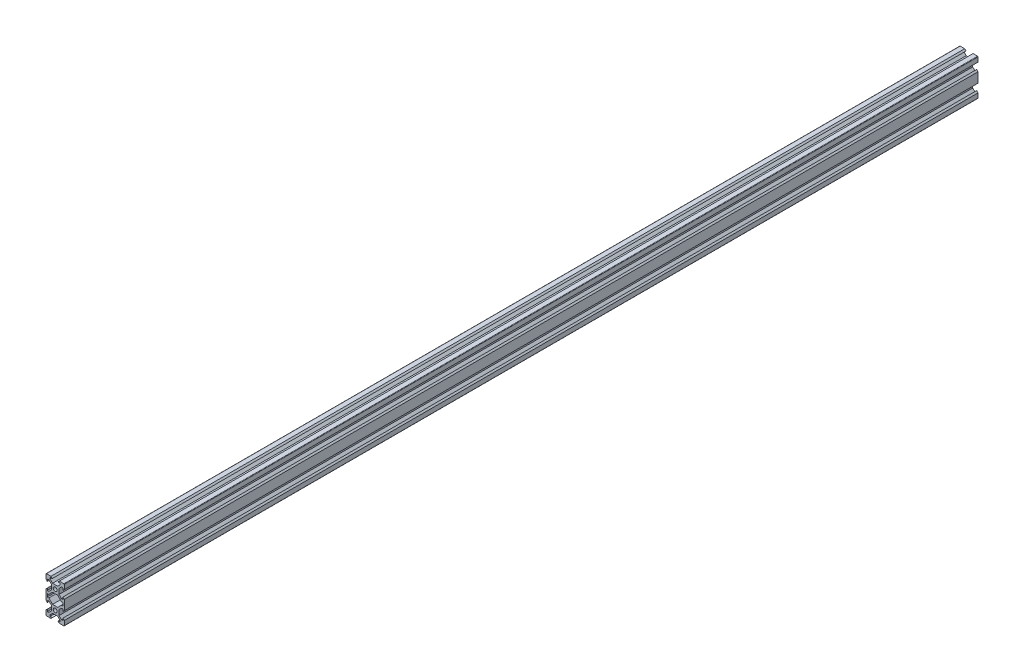
SolidWorks part; units mm, degrees
ref_plane "Front Plane" through (0, 0, 0) normal (0, 0, 1) x (1, 0, 0)
ref_plane "Top Plane" through (0, 0, 0) normal (0, 1, 0) x (1, 0, 0)
ref_plane "Right Plane" through (0, 0, 0) normal (1, 0, 0) x (0, 0, -1)
sketch "Sketch2" plane through (0, 0, 0) normal (0, 0, 1) x (1, 0, 0)
  line L0 (-4.58, -10) -> (-3.125, -8.545)
  line L1 (-9.5, -10) -> (9.5, -10)
  line L2 (-10, -9.5) -> (-10, 29.5)
  line L3 (-10, 10) -> (10, 10)
  line L4 (10, -9.5) -> (10, 29.5)
  line L5 (-10, -10) -> (10, 10) construction
  line L6 (-10, 10) -> (10, -10) construction
  line L7 (-3.125, -8.545) -> (-5.5, -8.545)
  line L8 (0, 4.8178) -> (0, -5.9385) construction
  line L9 (-8.545, 3.125) -> (-10, 4.58)
  line L10 (-8.545, 5.5) -> (-8.545, 3.125)
  line L11 (5.5, -8.545) -> (3.125, -8.545)
  line L12 (3.125, -8.545) -> (4.58, -10)
  line L13 (-3.125, -8.545) -> (3.125, -8.545) construction
  line L14 (-5.5, -8.545) -> (-5.5, -6.905)
  line L15 (-5.5, -6.905) -> (-2.84, -4.245)
  line L16 (-2.84, -4.245) -> (2.84, -4.245)
  line L17 (2.84, -4.245) -> (5.5, -6.905)
  line L18 (5.5, -6.905) -> (5.5, -8.545)
  line L19 (-6.905, 5.5) -> (-8.545, 5.5)
  line L20 (-4.245, 2.84) -> (-6.905, 5.5)
  line L21 (-10, -4.58) -> (-8.545, -3.125)
  line L22 (-8.545, -3.125) -> (-8.545, -5.5)
  line L23 (-8.545, -5.5) -> (-6.905, -5.5)
  line L24 (-6.905, -5.5) -> (-4.245, -2.84)
  line L25 (-4.245, -2.84) -> (-4.245, 2.84)
  line L26 (10, -4.58) -> (8.545, -3.125)
  line L27 (8.545, -3.125) -> (8.545, -5.5)
  line L28 (8.545, -5.5) -> (6.905, -5.5)
  line L29 (6.905, -5.5) -> (4.245, -2.84)
  line L30 (4.245, -2.84) -> (4.245, 2.84)
  line L31 (4.245, 2.84) -> (6.905, 5.5)
  line L32 (6.905, 5.5) -> (8.545, 5.5)
  line L33 (8.545, 3.125) -> (10, 4.58)
  line L34 (8.545, 5.5) -> (8.545, 3.125)
  line L35 (-3.7027, 0) -> (5.6465, 0) construction
  line L36 (-2.84, 4.245) -> (2.84, 4.245)
  line L37 (-2.84, 4.245) -> (-6.905, 8.31)
  line L38 (-6.905, 8.31) -> (-8.545, 8.31)
  line L39 (-8.545, 8.31) -> (-8.545, 11.69)
  line L40 (-8.545, 10) -> (8.545, 10)
  line L41 (8.545, 11.69) -> (8.545, 8.31)
  line L42 (8.545, 8.31) -> (6.905, 8.31)
  line L43 (6.905, 8.31) -> (2.84, 4.245)
  line L44 (-10, 4.58) -> (-10, -4.58)
  line L45 (10, 4.58) -> (10, -4.58)
  line L46 (-4.58, -10) -> (4.58, -10)
  line L47 (-3.7027, 20) -> (5.6465, 20) construction
  line L48 (-3.125, 28.545) -> (3.125, 28.545) construction
  line L49 (0, 15.1822) -> (0, 25.9385) construction
  line L50 (-10, 10) -> (10, 30) construction
  line L51 (-10, 30) -> (10, 10) construction
  line L52 (-4.58, 30) -> (4.58, 30)
  line L53 (10, 15.42) -> (10, 24.58)
  line L54 (-10, 15.42) -> (-10, 24.58)
  line L55 (6.905, 11.69) -> (2.84, 15.755)
  line L56 (8.545, 11.69) -> (6.905, 11.69)
  line L57 (-6.905, 11.69) -> (-8.545, 11.69)
  line L58 (-2.84, 15.755) -> (-6.905, 11.69)
  line L59 (-2.84, 15.755) -> (2.84, 15.755)
  line L60 (8.545, 14.5) -> (8.545, 16.875)
  line L61 (8.545, 16.875) -> (10, 15.42)
  line L62 (6.905, 14.5) -> (8.545, 14.5)
  line L63 (4.245, 17.16) -> (6.905, 14.5)
  line L64 (4.245, 22.84) -> (4.245, 17.16)
  line L65 (6.905, 25.5) -> (4.245, 22.84)
  line L66 (8.545, 25.5) -> (6.905, 25.5)
  line L67 (8.545, 23.125) -> (8.545, 25.5)
  line L68 (10, 24.58) -> (8.545, 23.125)
  line L69 (-4.245, 22.84) -> (-4.245, 17.16)
  line L70 (-6.905, 25.5) -> (-4.245, 22.84)
  line L71 (-8.545, 25.5) -> (-6.905, 25.5)
  line L72 (-8.545, 23.125) -> (-8.545, 25.5)
  line L73 (-10, 24.58) -> (-8.545, 23.125)
  line L74 (-4.245, 17.16) -> (-6.905, 14.5)
  line L75 (-6.905, 14.5) -> (-8.545, 14.5)
  line L76 (5.5, 26.905) -> (5.5, 28.545)
  line L77 (2.84, 24.245) -> (5.5, 26.905)
  line L78 (-2.84, 24.245) -> (2.84, 24.245)
  line L79 (-5.5, 26.905) -> (-2.84, 24.245)
  line L80 (-5.5, 28.545) -> (-5.5, 26.905)
  line L81 (3.125, 28.545) -> (4.58, 30)
  line L82 (5.5, 28.545) -> (3.125, 28.545)
  line L83 (-8.545, 14.5) -> (-8.545, 16.875)
  line L84 (-8.545, 16.875) -> (-10, 15.42)
  line L85 (-3.125, 28.545) -> (-5.5, 28.545)
  line L86 (-9.5, 30) -> (9.5, 30)
  line L87 (-4.58, 30) -> (-3.125, 28.545)
  circle A0 centre (0, 0) radius 2.1
  arc A1 (9.5, -10) -> (10, -9.5) centre (9.5, -9.5) ccw
  arc A2 (-9.5, -10) -> (-10, -9.5) centre (-9.5, -9.5) cw
  arc A3 (-9.5, 30) -> (-10, 29.5) centre (-9.5, 29.5) ccw
  arc A4 (9.5, 30) -> (10, 29.5) centre (9.5, 29.5) cw
  circle A5 centre (0, 20) radius 2.1
  point P15 (0, -8.545)
  point P18 (0, -4.245)
  dimension "D1" = 4.2
  dimension "D4" = 0.5
  dimension "D2" = 20
  dimension "D3" = 20
  dimension "D5" = 6.25
  dimension "D6" = 5.68
  dimension "D7" = 11
  dimension "D8" = 9.16
  dimension "D9" = 135
  dimension "D10" = 4.3
  dimension "D11" = 45
  dimension "D12" = 4.58
  dimension "D13" = 135
  dimension "D14" = 1.64
  dimension "D15" = 1.69
  dimension "D16" = 1.64
  dimension "D17" = 1.69
extrude "Boss-Extrude1" add sketch "Sketch2" along normal blind 1000 contours A4 L86 L81 L82 L76 L77 L78 L79 L80 L85 L87 A3 L2 L73 L72 L71 L70 L69 L74 L75 L83 L84 L3 L39 L57 L58 L59 L55 L56 L41 L4 L61 L60 L62 L63 L64 L65 L66 L67 L68 A5 | A2 L1 L0 L7 L14 L15 L16 L17 L18 L11 L12 A1 L4 L26 L27 L28 L29 L30 L31 L32 L34 L33 L3 L41 L42 L43 L36 L37 L38 L39 L2 L9 L10 L19 L20 L25 L24 L23 L22 L21 A0
